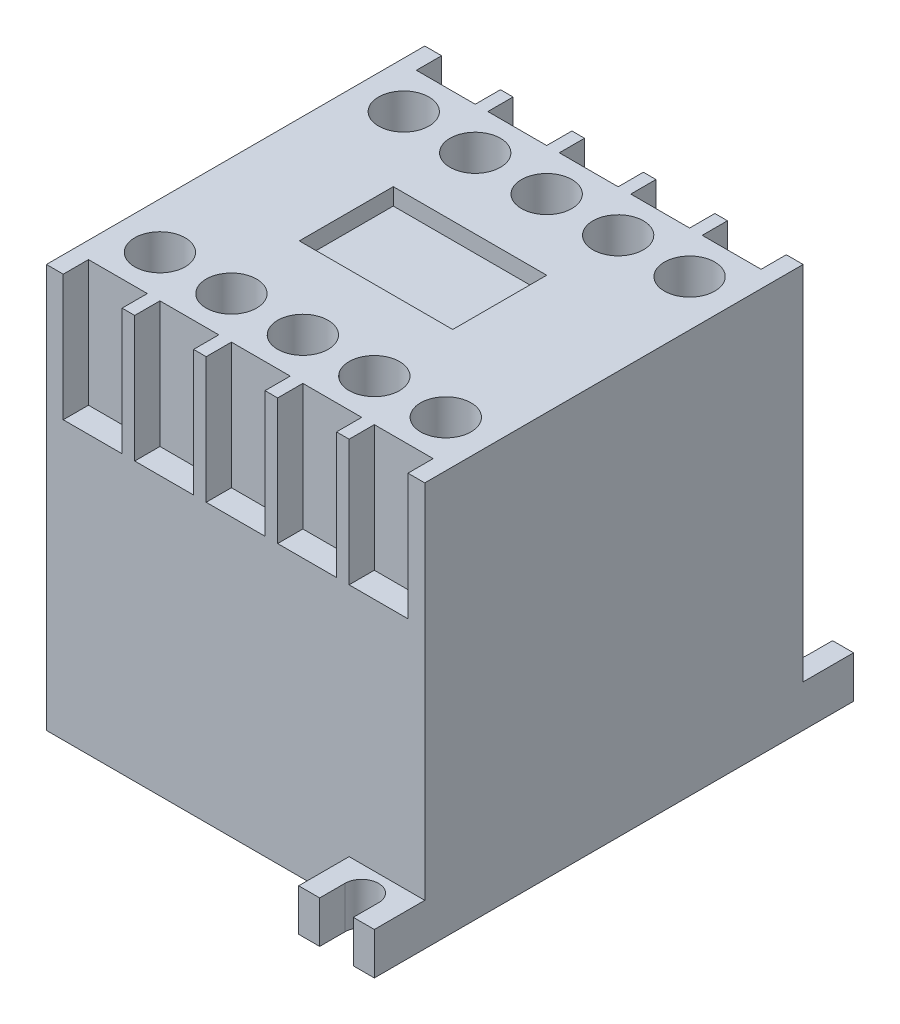
SolidWorks part; units mm, degrees
ref_plane "Front Plane" through (0, 0, 0) normal (0, 0, 1) x (1, 0, 0)
ref_plane "Top Plane" through (0, 0, 0) normal (0, 1, 0) x (1, 0, 0)
ref_plane "Right Plane" through (0, 0, 0) normal (1, 0, 0) x (0, 0, -1)
sketch "Sketch1" plane through (0, 0, 0) normal (0, 1, 0) x (1, 0, 0)
  line L1 (0, 0) -> (45, 0)
  line L2 (0, 0) -> (0, 45)
  line L3 (0, 45) -> (45, 45)
  line L4 (45, 0) -> (45, 45)
  dimension "D1" = 45
extrude "Boss-Extrude1" add sketch "Sketch1" along normal blind 48
sketch "Sketch2" plane through (0, 48, 0) normal (0, 1, 0) x (1, 0, 0)
  line L0 (0, 0) -> (45, 0) construction
  line L1 (2, 0) -> (9, 0)
  line L2 (2, 0) -> (2, 3)
  line L3 (2, 3) -> (9, 3)
  line L4 (9, 0) -> (9, 3)
  line L5 (0, 45) -> (0, 0) construction
  line L6 (10.5, 0) -> (10.5, 3)
  line L7 (10.5, 0) -> (17.5, 0)
  line L8 (17.5, 0) -> (17.5, 3)
  line L9 (10.5, 3) -> (17.5, 3)
  line L10 (19, 0) -> (19, 3)
  line L11 (19, 0) -> (26, 0)
  line L12 (26, 0) -> (26, 3)
  line L13 (19, 3) -> (26, 3)
  line L14 (27.5, 0) -> (27.5, 3)
  line L15 (27.5, 0) -> (34.5, 0)
  line L16 (34.5, 0) -> (34.5, 3)
  line L17 (27.5, 3) -> (34.5, 3)
  line L18 (36, 0) -> (36, 3)
  line L19 (36, 0) -> (43, 0)
  line L20 (43, 0) -> (43, 3)
  line L21 (36, 3) -> (43, 3)
  line L22 (0, 22.5) -> (45, 22.5) construction
  line L23 (45, 0) -> (45, 45) construction
  line L24 (36, 45) -> (43, 45)
  line L25 (43, 45) -> (43, 42)
  line L26 (36, 42) -> (43, 42)
  line L27 (36, 45) -> (36, 42)
  line L28 (27.5, 45) -> (34.5, 45)
  line L29 (34.5, 45) -> (34.5, 42)
  line L30 (27.5, 42) -> (34.5, 42)
  line L31 (27.5, 45) -> (27.5, 42)
  line L32 (19, 45) -> (26, 45)
  line L33 (26, 45) -> (26, 42)
  line L34 (19, 42) -> (26, 42)
  line L35 (19, 45) -> (19, 42)
  line L36 (10.5, 45) -> (17.5, 45)
  line L37 (17.5, 45) -> (17.5, 42)
  line L38 (10.5, 42) -> (17.5, 42)
  line L39 (10.5, 45) -> (10.5, 42)
  line L40 (2, 42) -> (9, 42)
  line L41 (9, 45) -> (9, 42)
  line L42 (2, 45) -> (9, 45)
  line L43 (2, 45) -> (2, 42)
  dimension "D1" = 2
  dimension "D2" = 7
  dimension "D3" = 3
  dimension "D4" = 5
extrude "Cut-Extrude1" cut sketch "Sketch2" against normal blind 15
sketch "Sketch3" plane through (0, 48, 0) normal (0, 1, 0) x (1, 0, 0)
  line L1 (9, 3) -> (2, 3) construction
  line L2 (9, 3) -> (2, 3) construction
  line L3 (0, 22.5) -> (45, 22.5) construction
  line L4 (0, 45) -> (0, 0) construction
  line L5 (45, 0) -> (45, 45) construction
  circle A0 centre (5.5, 8) radius 3
  circle A1 centre (14, 8) radius 3
  circle A2 centre (22.5, 8) radius 3
  circle A3 centre (31, 8) radius 3
  circle A4 centre (39.5, 8) radius 3
  circle A5 centre (39.5, 37) radius 3
  circle A6 centre (31, 37) radius 3
  circle A7 centre (22.5, 37) radius 3
  circle A8 centre (14, 37) radius 3
  circle A9 centre (5.5, 37) radius 3
  point P6 (5.5, 3)
  dimension "D1" = 6
  dimension "D2" = 5
  dimension "D3" = 5
extrude "Cut-Extrude2" cut sketch "Sketch3" against normal blind 8
sketch "Sketch4" plane through (0, 48, 0) normal (0, 1, 0) x (1, 0, 0)
  line L1 (12.613, 17.4612) -> (30.8626, 17.4612)
  line L2 (12.613, 17.4612) -> (12.613, 28.6397)
  line L3 (12.613, 28.6397) -> (30.8626, 28.6397)
  line L4 (30.8626, 17.4612) -> (30.8626, 28.6397)
extrude "Cut-Extrude3" cut sketch "Sketch4" against normal blind 2 contours L2 L1 L4 L3
sketch "Sketch5" plane through (0, 0, 0) normal (0, -1, 0) x (-1, 0, 0)
  line L0 (-42.5, 48) -> (-42.5, 51)
  line L1 (-45, 45) -> (-36, 45)
  line L2 (-45, 45) -> (-45, 51)
  line L3 (-45, 51) -> (-42.5, 51)
  line L4 (-36, 45) -> (-36, 51)
  line L5 (-38.5, 48) -> (-38.5, 51)
  line L6 (-38.5, 51) -> (-36, 51)
  line L7 (-45, 22.5) -> (0, 22.5) construction
  line L8 (-45, 0) -> (-45, 45) construction
  line L9 (0, 45) -> (0, 0) construction
  line L10 (-45, 0) -> (-36, 0)
  line L11 (-36, 0) -> (-36, -6)
  line L12 (-38.5, -6) -> (-36, -6)
  line L13 (-38.5, -3) -> (-38.5, -6)
  line L14 (-42.5, -3) -> (-42.5, -6)
  line L15 (-45, -6) -> (-42.5, -6)
  line L16 (-45, 0) -> (-45, -6)
  arc A0 (-42.5, 48) -> (-38.5, 48) centre (-40.5, 48) ccw
  arc A1 (-42.5, -3) -> (-38.5, -3) centre (-40.5, -3) cw
  point P9 (-45, 48)
  dimension "D1" = 4
  dimension "D2" = 9
  dimension "D3" = 6
extrude "Boss-Extrude2" add sketch "Sketch5" against normal blind 5
